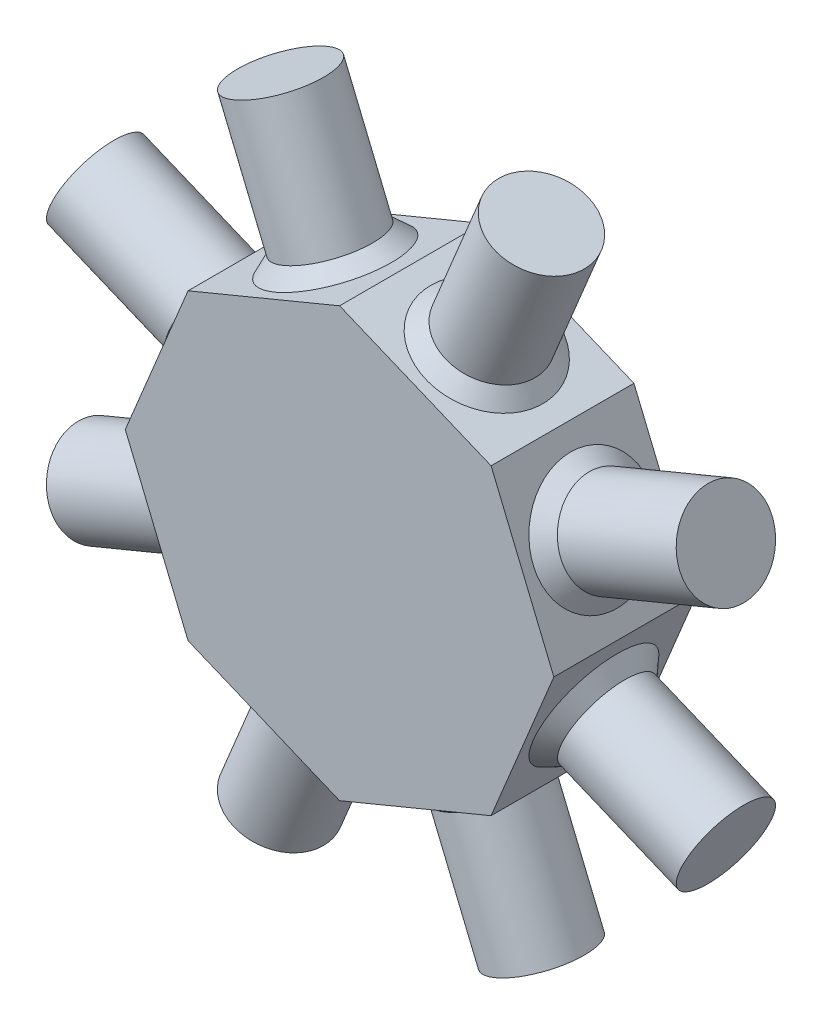
SolidWorks part; units mm, degrees
ref_plane "Front Plane" through (0, 0, 0) normal (0, 0, 1) x (1, 0, 0)
ref_plane "Top Plane" through (0, 0, 0) normal (0, 1, 0) x (1, 0, 0)
ref_plane "Right Plane" through (0, 0, 0) normal (1, 0, 0) x (0, 0, -1)
sketch "Sketch1" plane through (0, 0, 0) normal (0, 0, 1) x (1, 0, 0)
  circle A0 centre (0, 0) radius 38.1
  dimension "D1" = 76.2
extrude "Boss-Extrude1" add sketch "Sketch1" along normal mid plane 25.4
sketch "Sketch2" plane through (0, 0, 12.7) normal (0, 0, 1) x (1, 0, 0)
  line L0 (38.1, 0) -> (26.9408, 26.9408)
  line L1 (0, 38.1) -> (-26.9408, 26.9408)
  line L2 (-26.9408, 26.9408) -> (-38.1, 0)
  line L3 (-38.1, 0) -> (-26.9408, -26.9408)
  line L4 (-26.9408, -26.9408) -> (0, -38.1)
  line L5 (0, -38.1) -> (26.9408, -26.9408)
  line L6 (26.9408, -26.9408) -> (38.1, 0)
  line L7 (26.9408, 26.9408) -> (0, 38.1)
  circle A0 centre (0, 0) radius 35.1998 construction
  circle A1 centre (0, 0) radius 38.1 construction
extrude "Cut-Extrude1" cut sketch "Sketch2" against normal blind 25.4 flip side to cut
sketch "Sketch3" plane through (13.4704, 32.5204, 0) normal (0.3827, 0.9239, 0) x (0.9239, -0.3827, 0)
  line L0 (14.5802, 12.7) -> (-14.5802, 12.7) construction
  circle A0 centre (0, 0) radius 8.255
  point P4 (0, 12.7)
  dimension "D2" = 16.51
  dimension "D1" = 12.7
extrude "Boss-Extrude2" add sketch "Sketch3" along normal blind 25.4
sketch3d "3DSketch1"
  line L0 (0, 0, 12.7) -> (0, 0, -12.7)
pattern_circular "CirPattern4" count 8 over 360 about axis through (0, 0, 0) along (0, 0, 1) of "Boss-Extrude2"
chamfer "Chamfer2" distance 2.54 angle 45 8 edges at (5.8438, 35.6794, 0) (29.3613, 21.097, 0) (35.6794, -5.8438, 0) (21.097, -29.3613, 0) (-5.8438, -35.6794, 0) (-29.3613, -21.097, 0) (-35.6794, 5.8438, 0) (-21.097, 29.3613, 0)
